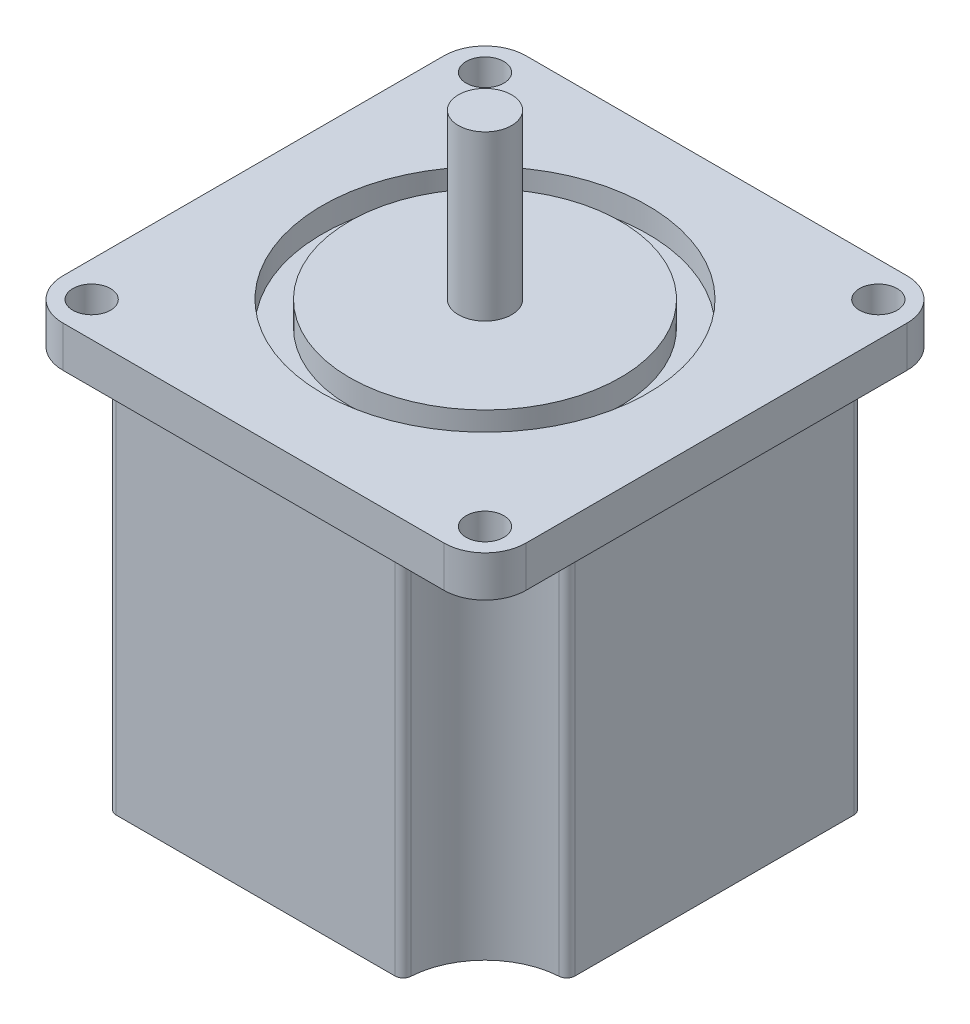
SolidWorks part; units mm, degrees
ref_plane "Front Plane" through (0, 0, 0) normal (0, 0, 1) x (1, 0, 0)
ref_plane "Top Plane" through (0, 0, 0) normal (0, 1, 0) x (1, 0, 0)
ref_plane "Right Plane" through (0, 0, 0) normal (1, 0, 0) x (0, 0, -1)
sketch "Sketch1" plane through (0, 0, 0) normal (0, 1, 0) x (1, 0, 0)
  line L1 (-28, 28) -> (28, 28)
  line L2 (-28, 28) -> (-28, -28)
  line L3 (-28, -28) -> (28, -28)
  line L4 (28, 28) -> (28, -28)
  line L5 (-28, 28) -> (28, -28) construction
  line L6 (-28, -28) -> (28, 28) construction
  point P0 (0, 0)
  dimension "D1" = 56
extrude "Boss-Extrude1" add sketch "Sketch1" along normal blind 44
sketch "Sketch2" plane through (0, 44, 0) normal (0, 1, 0) x (1, 0, 0)
  line L0 (-24, 24) -> (24, 24) construction
  line L1 (-28.25, 28.25) -> (28.25, 28.25)
  line L2 (-28.25, 28.25) -> (-28.25, -28.25)
  line L3 (-28.25, -28.25) -> (28.25, -28.25)
  line L4 (28.25, 28.25) -> (28.25, -28.25)
  line L5 (-28.25, 28.25) -> (28.25, -28.25) construction
  line L6 (-28.25, -28.25) -> (28.25, 28.25) construction
  line L15 (24, 24) -> (-24, -24) construction
  line L16 (24, -24) -> (-24, 24) construction
  line L17 (24, 24) -> (24, -24) construction
  line L18 (24, -24) -> (-24, -24) construction
  line L19 (-24, -24) -> (-24, 24) construction
  circle A0 centre (-24, 24) radius 2.3
  circle A1 centre (24, 24) radius 2.3
  circle A2 centre (-24, -24) radius 2.3
  circle A3 centre (24, -24) radius 2.3
  point P0 (0, 0)
  point P6 (0, 0)
  point P15 (0, 0)
  dimension "D1" = 4.6
  dimension "D2" = 4.6
  dimension "D3" = 4.6
  dimension "D4" = 4.6
  dimension "D5" = 56.5
  dimension "D6" = 56.5
  dimension "D7" = 48
extrude "Boss-Extrude2" add sketch "Sketch2" along normal blind 5
sketch "Sketch3" plane through (0, 49, 0) normal (0, 1, 0) x (1, 0, 0)
  circle A0 centre (0, 0) radius 16.5289
  circle A1 centre (0, 0) radius 19.8517
extrude "Cut-Extrude1" cut sketch "Sketch3" against normal blind 3
sketch "Sketch4" plane through (0, 49, 0) normal (0, 1, 0) x (1, 0, 0)
  circle A0 centre (0, 0) radius 3.25
  dimension "D1" = 6.5
extrude "Boss-Extrude3" add sketch "Sketch4" along normal blind 20
sketch "Sketch5" plane through (0, 0, 0) normal (0, -1, 0) x (1, 0, 0)
  line L0 (-28, -28) -> (-28, 28) construction
  line L1 (-28, 28) -> (28, 28) construction
  line L2 (-28, 18) -> (-28, 28)
  line L3 (-28, 28) -> (-18, 28)
  arc A0 (-28, 18) -> (-18, 28) centre (-27.6799, 27.6799) ccw
  dimension "D1" = 10
  dimension "D2" = 10
extrude "Cut-Extrude2" cut sketch "Sketch5" against normal blind 44
mirror "Mirror1" about plane through (0, 0, 0) normal (1, 0, 0) of "Cut-Extrude2" second plane through (0, 0, 0) second plane normal (0, 0, 1)
fillet "Fillet3" radius 1 8 edges at (-18, 22, 28) (-28, 22, 18) (-28, 22, -18) (-18, 22, -28) (28, 22, 18) (18, 22, 28) (18, 22, -28) (28, 22, -18)
fillet "Fillet2" radius 5 4 edges at (28.25, 46.5, -28.25) (-28.25, 46.5, -28.25) (28.25, 46.5, 28.25) (-28.25, 46.5, 28.25)
